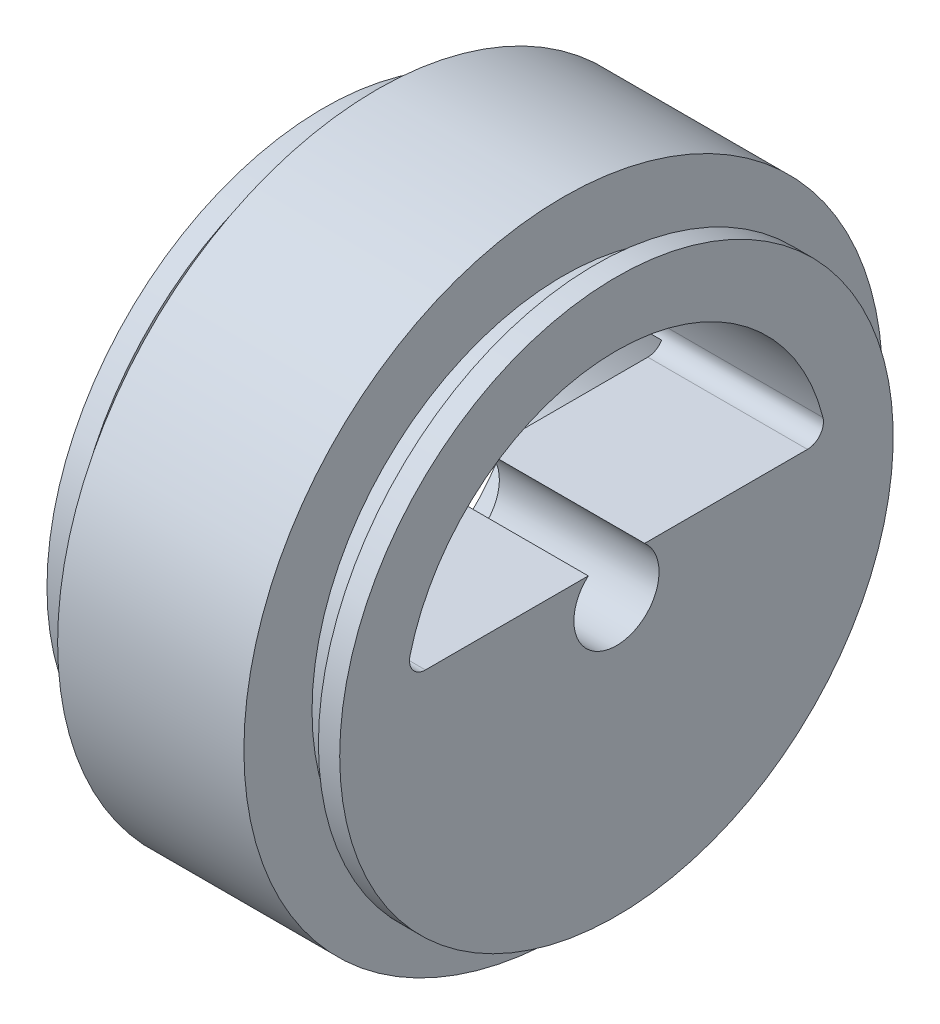
SolidWorks part; units mm, degrees
ref_plane "Plan de face" through (0, 0, 0) normal (0, 0, 1) x (1, 0, 0)
ref_plane "Plan de dessus" through (0, 0, 0) normal (0, 1, 0) x (1, 0, 0)
ref_plane "Plan de droite" through (0, 0, 0) normal (1, 0, 0) x (0, 0, -1)
sketch "Esquisse1" plane through (0, 0, 0) normal (0, 0, 1) x (1, 0, 0)
  line L0 (-2.5, 19.6) -> (-2.5, 26)
  line L1 (2.5, 30) -> (20, 30)
  line L2 (-0.5, 23.6) -> (2.5, 23.6)
  line L3 (0, 23.6) -> (20, 23.6) construction
  line L4 (-0.5, 23.6) -> (-0.5, 26)
  line L5 (25, 26) -> (23, 26)
  line L7 (-2.5, 26) -> (-0.5, 26)
  line L8 (23, 23.6) -> (23, 26)
  line L9 (23, 23.6) -> (20, 23.6)
  line L10 (-2.5, -1.9975) -> (-2.5, 33.1761) construction
  line L11 (-0.5, -1.9975) -> (-0.5, 33.1761) construction
  line L12 (20, 23.6) -> (20, 30)
  line L13 (0, 30) -> (20, 30) construction
  line L14 (2.5, 23.6) -> (2.5, 30)
  line L15 (10, 4) -> (10, 19.6)
  line L16 (25, 4) -> (25, 26)
  line L17 (10, 0) -> (26.9465, 0) construction
  line L18 (10, -1.9975) -> (10, 26) construction
  line L19 (25, -1.9975) -> (25, 26) construction
  line L20 (10, 4) -> (25, 4)
  line L21 (-2.5, 19.6) -> (10, 19.6)
  line L22 (-0.5, 19.6) -> (2.5, 19.6) construction
  line L23 (10, 4) -> (26.9465, 4) construction
revolve "Révolution1" add sketch "Esquisse1" angle 360 about L17
sketch "Esquisse2" plane through (25, 0, 0) normal (1, 0, 0) x (0, 0, -1)
  line L1 (17.9444, 3) -> (-17.9444, 3)
  arc A1 (19.3993, 4.8649) -> (-19.3993, 4.8649) centre (0, 0) ccw
  arc A2 (-17.9444, 3) -> (-19.3993, 4.8649) centre (-17.9444, 4.5) cw
  arc A3 (17.9444, 3) -> (19.3993, 4.8649) centre (17.9444, 4.5) ccw
extrude "Extrusion1" cut sketch "Esquisse2" against normal through all
